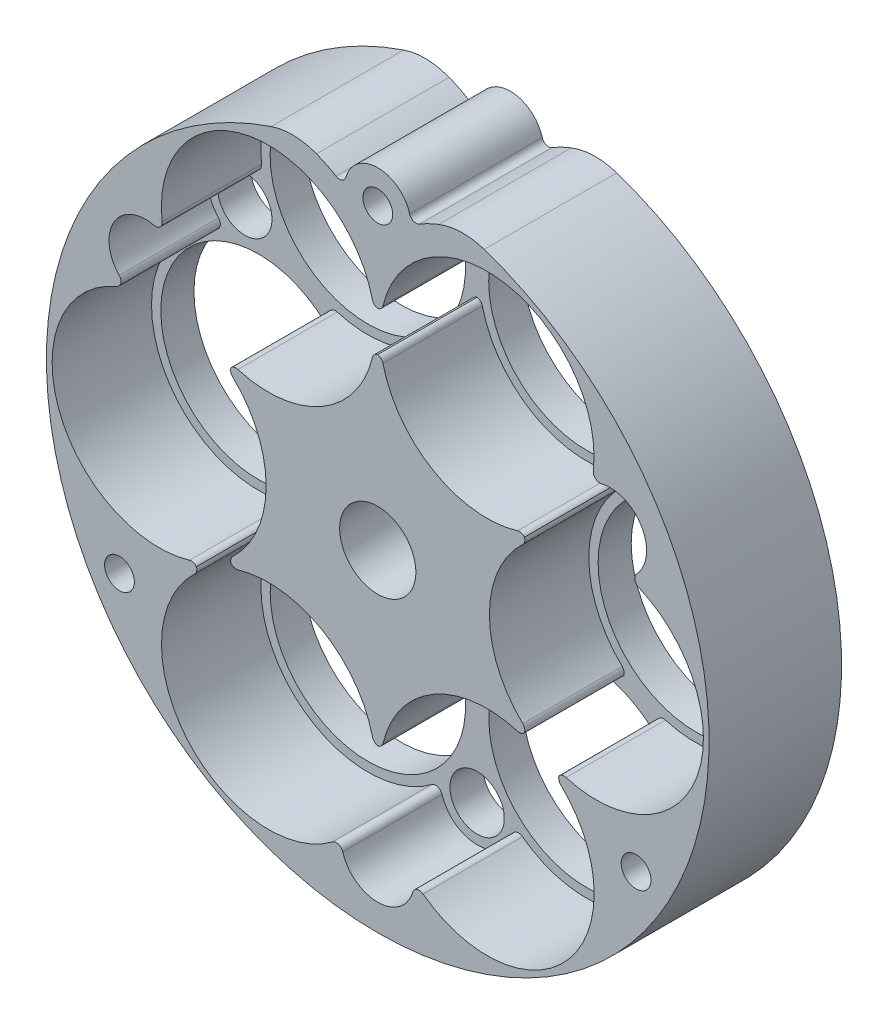
SolidWorks part; units mm, degrees
ref_plane "前视基准面" through (0, 0, 0) normal (0, 0, 1) x (1, 0, 0)
ref_plane "上视基准面" through (0, 0, 0) normal (0, 1, 0) x (1, 0, 0)
ref_plane "右视基准面" through (0, 0, 0) normal (1, 0, 0) x (0, 0, -1)
ref_plane "基准面4" through (0, 0, 0) normal (0, 0, -1) x (-1, 0, 0)
sketch "草图1" plane through (0, 0, 0) normal (0, 0, -1) x (-1, 0, 0)
  arc A0 (-163.0448, 48.2683) -> (-136.9283, 48.2611) centre (-150, 0) ccw
  arc A1 (-136.9283, 48.2611) -> (-143.7158, 45.7512) centre (-133.5, 28.5571) ccw
  arc A2 (-143.7158, 45.7512) -> (-145.1899, 46.3424) centre (-144.2266, 46.6109) cw
  arc A3 (-145.1899, 46.3424) -> (-154.8183, 46.3582) centre (-150.0063, 45) ccw
  arc A4 (-154.8183, 46.3582) -> (-156.2908, 45.7697) centre (-155.7807, 46.6298) cw
  arc A5 (-156.2908, 45.7697) -> (-163.0448, 48.2683) centre (-166.4937, 28.568) ccw
extrude "凸台-拉伸1" add sketch "草图1" against normal blind 20
sketch "草图2" plane through (0, 0, 20) normal (0, 0, 1) x (1, 0, 0)
  arc A0 (182.5305, 26.6588) -> (150.7928, 32.35) centre (166.4937, 28.568) ccw
  arc A1 (150.7928, 32.35) -> (149.9959, 31.5997) centre (149.8206, 32.5842) cw
  arc A2 (149.9959, 31.5997) -> (149.1984, 32.3495) centre (150.1704, 32.5843) cw
  arc A3 (149.1984, 32.3495) -> (117.46, 26.6749) centre (133.5, 28.5571) ccw
  arc A4 (117.46, 26.6749) -> (116.2327, 25.5862) centre (116.4669, 26.5584) cw
  arc A5 (116.2327, 25.5862) -> (110.9752, 16.4323) centre (114.9448, 20.2391) ccw
  arc A6 (110.9752, 16.4323) -> (110.6476, 14.8211) centre (110.2535, 15.7401) cw
  arc A7 (110.6476, 14.8211) -> (121.5978, -15.5072) centre (117.0126, -0.0218) ccw
  arc A8 (121.5978, -15.5072) -> (122.645, -15.82) centre (121.8817, -16.466) cw
  arc A9 (122.645, -15.82) -> (122.3929, -16.8835) centre (121.704, -16.1586) cw
  arc A10 (122.3929, -16.8835) -> (143.1688, -41.5397) centre (133.5189, -28.5897) ccw
  arc A11 (143.1688, -41.5397) -> (144.7253, -42.0582) centre (143.7663, -42.3415) cw
  arc A12 (144.7253, -42.0582) -> (155.2816, -42.0344) centre (150, -40.5) ccw
  arc A13 (155.2816, -42.0344) -> (156.8408, -41.5125) centre (156.2419, -42.3133) cw
  arc A14 (156.8408, -41.5125) -> (177.6231, -16.858) centre (166.5126, -28.5788) ccw
  arc A15 (177.6231, -16.858) -> (177.369, -15.7967) centre (178.3111, -16.1322) cw
  arc A16 (177.369, -15.7967) -> (178.4149, -15.4855) centre (178.131, -16.4443) cw
  arc A17 (178.4149, -15.4855) -> (189.39, 14.8321) centre (183, 0) ccw
  arc A18 (189.39, 14.8321) -> (189.0608, 16.4394) centre (189.7857, 15.7505) cw
  arc A19 (189.0608, 16.4394) -> (183.762, 25.5694) centre (185.074, 20.2282) ccw
  arc A20 (183.762, 25.5694) -> (182.5305, 26.6588) centre (183.5235, 26.5406) cw
extrude "切除-拉伸1" cut sketch "草图2" against normal blind 15
sketch "草图3" plane through (0, 0, 5) normal (0, 0, 1) x (1, 0, 0)
  arc A0 (150.8067, -24.8173) -> (150.0147, -25.5679) centre (149.8342, -24.5843) cw
  arc A1 (150.0147, -25.5679) -> (149.2222, -24.8178) centre (150.1945, -24.5842) cw
  arc A2 (149.2222, -24.8178) -> (128.9135, -13.1103) centre (133.5189, -28.5897) ccw
  arc A3 (128.9135, -13.1103) -> (127.8685, -12.8019) centre (128.6283, -12.1518) cw
  arc A4 (127.8685, -12.8019) -> (128.1232, -11.7425) centre (128.8112, -12.4683) cw
  arc A5 (128.1232, -11.7425) -> (128.1078, 11.7136) centre (117.0126, -0.0218) ccw
  arc A6 (128.1078, 11.7136) -> (127.851, 12.7707) centre (128.7948, 12.4402) cw
  arc A7 (127.851, 12.7707) -> (128.8947, 13.0776) centre (128.6096, 12.1191) cw
  arc A8 (128.8947, 13.0776) -> (149.2107, 24.816) centre (133.5, 28.5571) ccw
  arc A9 (149.2107, 24.816) -> (149.9978, 25.567) centre (150.1835, 24.5843) cw
  arc A10 (149.9978, 25.567) -> (150.7855, 24.8165) centre (149.8128, 24.5842) cw
  arc A11 (150.7855, 24.8165) -> (171.0991, 13.0885) centre (166.4937, 28.568) ccw
  arc A12 (171.0991, 13.0885) -> (172.1441, 12.7801) centre (171.3843, 12.13) cw
  arc A13 (172.1441, 12.7801) -> (171.8894, 11.7208) centre (171.2014, 12.4465) cw
  arc A14 (171.8894, 11.7208) -> (171.8895, -11.7209) centre (183, 0) ccw
  arc A15 (171.8895, -11.7209) -> (172.1435, -12.7821) centre (171.2015, -12.4466) cw
  arc A16 (172.1435, -12.7821) -> (171.0976, -13.0934) centre (171.3815, -12.1345) cw
  arc A17 (171.0976, -13.0934) -> (150.8067, -24.8173) centre (166.5126, -28.5788) ccw
extrude "凸台-拉伸2" add sketch "草图3" along normal blind 15
hole_wizard "Ø11.5 (11.5) 直径孔1" positions "草图5" profile "草图4" hole size "Ø11.5" standard "ANSI Metric"
sketch "草图5" plane through (0, 0, 0) normal (0, 0, -1) x (-1, 0, 0)
  point P0 (-150, 0)
sketch "草图4" plane through (150, 0, 0) normal (1, 0, 0) x (0, 1, 0)
  line L0 (0, 0) -> (0, 20)
  line L1 (0, 20) -> (5.75, 20)
  line L2 (5.75, 20) -> (5.75, 0)
  line L5 (5.75, 0) -> (0, 0)
  line L11 (0, -6.35) -> (0, 107.95) construction
  dimension "通孔孔直径" = 11.5
  dimension "通孔孔深度" = 20
hole_wizard "Ø4.5 (4.5) 直径孔1" positions "草图7" profile "草图6" hole size "Ø4.5" standard "ANSI Metric"
sketch "草图7" plane through (0, 0, 0) normal (0, 0, -1) x (-1, 0, 0)
  point P0 (-150.0063, 45)
  point P1 (-111.0257, -22.5163)
  point P2 (-188.9869, -22.5163)
sketch "草图6" plane through (150.0063, 45, 0) normal (1, 0, 0) x (0, 1, 0)
  line L0 (0, 0) -> (0, 20)
  line L1 (0, 20) -> (2.25, 20)
  line L2 (2.25, 20) -> (2.25, 0)
  line L5 (2.25, 0) -> (0, 0)
  line L11 (0, -6.35) -> (0, 107.95) construction
  dimension "通孔孔直径" = 4.5
  dimension "通孔孔深度" = 20
hole_wizard "Ø8.2 (8.2) 直径孔1" positions "草图9" profile "草图8" hole size "Ø8.2" standard "ANSI Metric"
sketch "草图9" plane through (0, 0, 0) normal (0, 0, -1) x (-1, 0, 0)
  point P0 (-150, -40.5)
  point P1 (-114.9448, 20.2391)
  point P2 (-185.074, 20.2282)
sketch "草图8" plane through (150, -40.5, 0) normal (1, 0, 0) x (0, 1, 0)
  line L0 (0, 0) -> (0, 20)
  line L1 (0, 20) -> (4.1, 20)
  line L2 (4.1, 20) -> (4.1, 0)
  line L5 (4.1, 0) -> (0, 0)
  line L11 (0, -6.35) -> (0, 107.95) construction
  dimension "通孔孔直径" = 8.2
  dimension "通孔孔深度" = 20
hole_wizard "M27 间隙孔1" positions "草图11" profile "草图10" hole size "M27" standard "ANSI Metric"
sketch "草图11" plane through (0, 0, 0) normal (0, 0, -1) x (-1, 0, 0)
  point P0 (-183, 0)
  point P1 (-166.5126, -28.5788)
  point P2 (-133.5189, -28.5897)
  point P3 (-166.4937, 28.568)
  point P4 (-117.0126, -0.0218)
  point P5 (-133.5, 28.5571)
sketch "草图10" plane through (183, 0, 0) normal (1, 0, 0) x (0, 1, 0)
  line L0 (0, 0) -> (0, 20)
  line L1 (0, 20) -> (14.75, 20)
  line L2 (14.75, 20) -> (14.75, 0)
  line L5 (14.75, 0) -> (0, 0)
  line L11 (0, -6.35) -> (0, 107.95) construction
  dimension "通孔孔直径" = 29.5
  dimension "通孔孔深度" = 20
fillet "圆角1" radius 10 2 edges at (163.0448, 48.2683, 10) (136.9283, 48.2611, 10)
